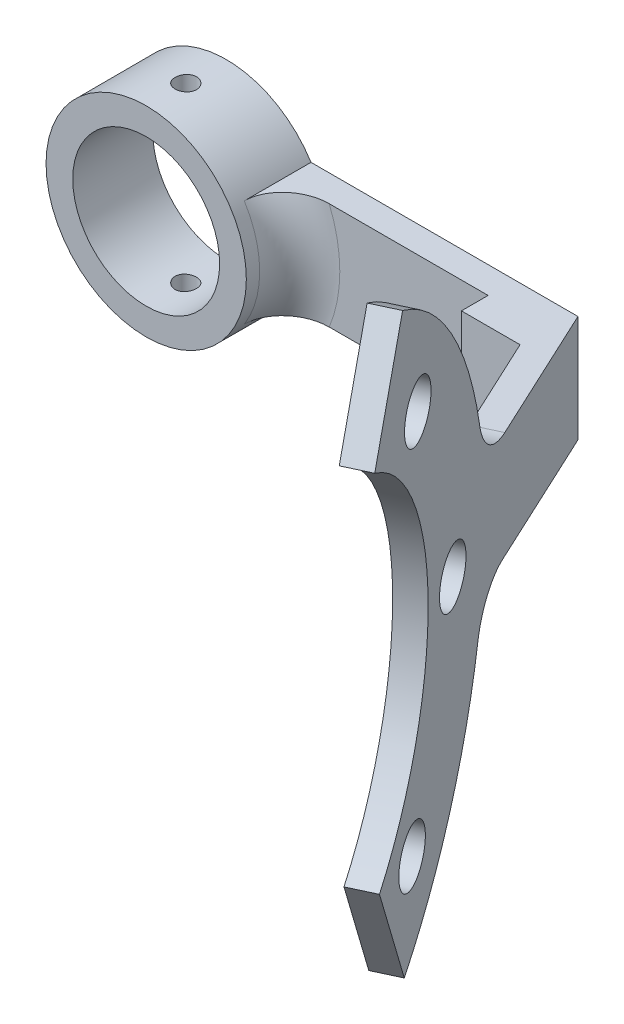
SolidWorks part; units mm, degrees
material "201 Annealed Stainless Steel (SS)"
ref_plane "Front Plane" through (0, 0, 0) normal (0, 0, 1) x (1, 0, 0)
ref_plane "Top Plane" through (0, 0, 0) normal (0, 1, 0) x (1, 0, 0)
ref_plane "Right Plane" through (0, 0, 0) normal (1, 0, 0) x (0, 0, -1)
sketch "Sketch1" plane through (0, 0, 0) normal (0, 1, 0) x (1, 0, 0)
  line L0 (0, 0) -> (0, 2)
  line L3 (34.5181, -15.55) -> (32.7602, -16.5037)
  line L6 (0, 0) -> (21.6058, 0)
  line L7 (25.997, -2) -> (32.7602, -16.5037)
  line L8 (26.3344, 2) -> (34.5181, -15.55)
  line L9 (0, 2) -> (26.3344, 2)
  line L10 (21.6058, 0) -> (21.6058, -2)
  line L11 (21.6058, -2) -> (25.997, -2)
  dimension "D1" = 2
  dimension "D2" = 2
  dimension "D3" = 115
  dimension "D4" = 2
extrude "Boss-Extrude1" add sketch "Sketch1" along normal blind 8
sketch "Sketch5" plane through (22.397, 0, -10.4439) normal (0.9063, 0, -0.4226) x (-0.4226, 0, -0.9063)
  line L0 (-40.7809, 18.7361) -> (-36.4672, 26.4289)
  line L1 (-40.0493, -9.0573) -> (-36.2057, -17.037)
  line L2 (-32.5193, 4.1187) -> (-28.7015, 4) construction
  arc A0 (-36.2057, -17.037) -> (-36.4672, 26.4289) centre (-48.6919, 4.6216) ccw
  arc A1 (-38.3829, -12.5169) -> (-38.9127, 22.0677) centre (-48.6919, 4.6216) ccw construction
  arc A2 (-40.0493, -9.0573) -> (-40.7809, 18.7361) centre (-48.6919, 4.6216) ccw
  dimension "D5" = 25
  dimension "D1" = 125
  dimension "D2" = 62.5
extrude "Boss-Extrude2" add sketch "Sketch5" against normal blind 2 contours L1 A0 L0 A2
sketch "Sketch3" plane through (20.5877, 0, -9.6002) normal (-0.9063, 0, 0.4226) x (0.4226, 0, 0.9063)
  circle A0 centre (28.7015, 4) radius 2.05
  circle A1 centre (48.6919, 4.6216) radius 20 construction
  circle A2 centre (34.117, 18.3174) radius 2.05
  circle A3 centre (48.0703, 24.6119) radius 2.05
  circle A4 centre (62.3876, 19.1964) radius 2.05
  circle A5 centre (68.6822, 5.2431) radius 2.05
  circle A6 centre (63.2667, -9.0742) radius 2.05
  circle A7 centre (49.3134, -15.3688) radius 2.05
  circle A8 centre (34.9961, -9.9533) radius 2.05
  point P23 (48.6919, 4.6216)
  dimension "D1" = 4.1
  dimension "D3" = 8
extrude "Cut-Extrude3" cut sketch "Sketch3" against normal blind 10 and the other way blind 10
fillet "Fillet2" radius 4 2 edges at (31.687, 0, 11.8406) (31.6019, 8, 11.6579)
sketch "Sketch6" plane through (0, 0, -2) normal (0, 0, -1) x (-1, 0, 0)
  line L0 (0, 8) -> (0, 0) construction
  circle A0 centre (0, 4) radius 7.5
  dimension "D1" = 15
extrude "Boss-Extrude3" add sketch "Sketch6" against normal blind 6
sketch "Sketch2" plane through (0, 0, 0) normal (0, 0, 1) x (1, 0, 0)
  circle A2 centre (0, 4) radius 5.5
  dimension "D1" = 11
extrude "Cut-Extrude4" cut sketch "Sketch2" against normal through all and the other way through all
ref_plane "Plane1" through (0, -3.5, 0) normal (0, -1, 0) x (-1, 0, 0)
sketch "Sketch8" plane through (0, -3.5, 0) normal (0, -1, 0) x (-1, 0, 0)
  circle A0 centre (0, -1.034) radius 0.8
  dimension "D1" = 1.6
extrude "Cut-Extrude5" cut sketch "Sketch8" against normal through all contours A0
fillet "Fillet3" radius 3 1 edges at (7.5, 4, 0)
equation "\"D2@Sketch5\"=\"D1@Sketch5\"/2"
